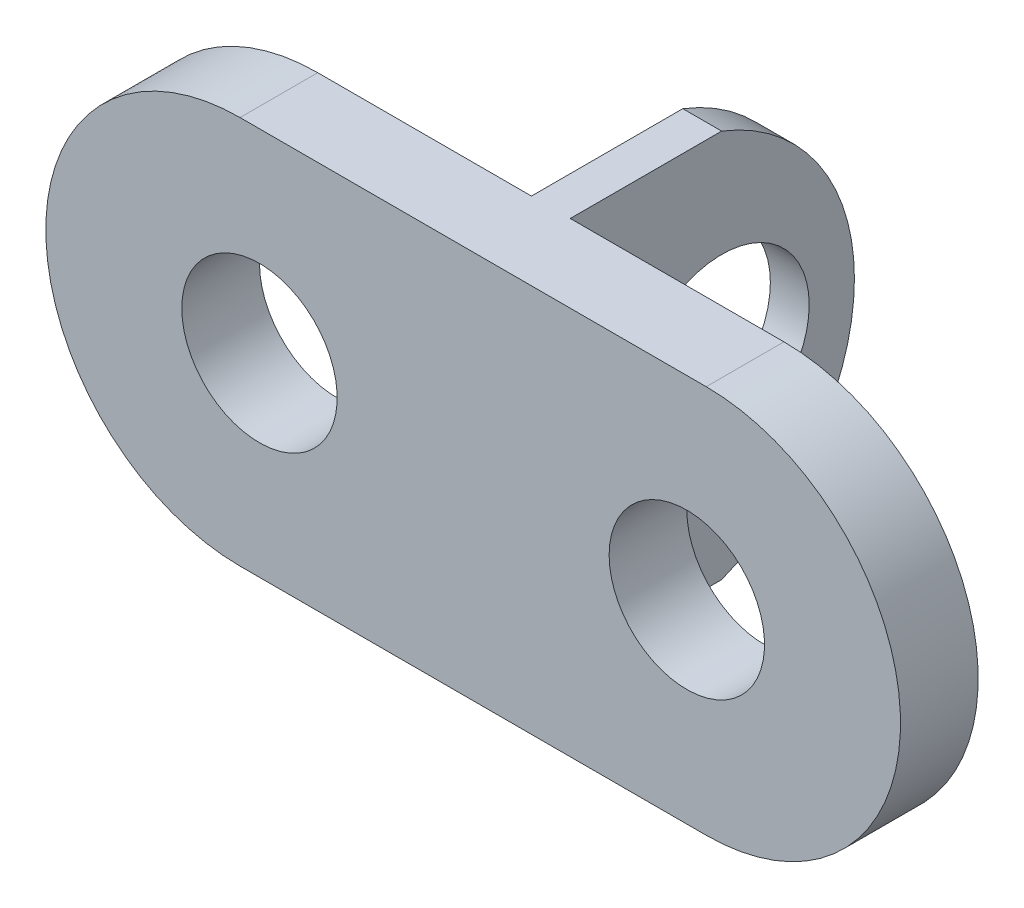
SolidWorks part; units mm, degrees
ref_plane "Front Plane" through (0, 0, 0) normal (0, 0, 1) x (1, 0, 0)
ref_plane "Top Plane" through (0, 0, 0) normal (0, 1, 0) x (1, 0, 0)
ref_plane "Right Plane" through (0, 0, 0) normal (1, 0, 0) x (0, 0, -1)
sketch "Esquisse1" plane through (0, 0, 0) normal (0, 0, 1) x (1, 0, 0)
  line L0 (-2.7952, 5.0683) -> (21.2048, 5.0683)
  line L1 (-2.7952, -14.9317) -> (21.2048, -14.9317)
  arc A0 (-2.7952, 5.0683) -> (-2.7952, -14.9317) centre (-2.7952, -4.9317) ccw
  arc A1 (21.2048, 5.0683) -> (21.2048, -14.9317) centre (21.2048, -4.9317) cw
  dimension "D2" = 10
  dimension "D1" = 24
  dimension "24" = 20
extrude "Boss.-Extru.1" add sketch "Esquisse1" along normal blind 4
sketch "Esquisse2" plane through (0, 0, 0) normal (0, 0, 1) x (1, 0, 0)
  line L0 (8.2048, 5.0683) -> (8.2048, -14.9317)
  line L1 (21.2048, 5.0683) -> (-2.7952, 5.0683) construction
  line L2 (-2.7952, -14.9317) -> (21.2048, -14.9317) construction
  line L3 (8.2048, -14.9317) -> (10.2048, -14.9317)
  line L4 (10.2048, -14.9317) -> (10.2048, 5.0683)
  line L5 (10.2048, 5.0683) -> (8.2048, 5.0683)
  dimension "D1" = 2
  dimension "D2" = 11
extrude "Boss.-Extru.2" add sketch "Esquisse2" against normal blind 15
sketch "Esquisse3" plane through (10.2048, 0, 0) normal (1, 0, 0) x (0, 0, -1)
  line L1 (15, 5.0683) -> (0, 5.0683) construction
  line L2 (15, -14.9317) -> (15, 5.0683) construction
  line L3 (0, 5.0683) -> (15, 5.0683)
  line L4 (0, 11) -> (0, -11) construction
  line L5 (15, 5.0683) -> (15, -14.9317)
  line L6 (15, -14.9317) -> (0, -14.9317)
  line L7 (15, -14.9317) -> (0, -14.9317) construction
  circle A0 centre (7.8, -4.9317) radius 4.5
  arc A2 (0, 5.0683) -> (0, -14.9317) centre (3.8962, -4.9317) cw
  line M3 (15, -14.9317) -> (15, 5.0683)
  line M4 (15, 5.0683) -> (0, 5.0683)
  dimension "D1" = 9
  dimension "D2" = 10
  dimension "7.2" = 7.2
extrude "Enlèv. mat.-Extru.1" cut sketch "Esquisse3" against normal through all contours A0 | A2 L6 M3 M4
sketch "Esquisse4" plane through (0, 0, 0) normal (0, 0, -1) x (-1, 0, 0)
  line L1 (-21.2048, 5.0683) -> (-10.2048, 5.0683) construction
  line L3 (-10.2048, -14.9317) -> (-10.2048, 5.0683) construction
  circle A1 centre (-20.2048, -4.9317) radius 4
  dimension "D1" = 8
  dimension "D2" = 10
  dimension "D3" = 10
extrude "Enlèv. mat.-Extru.2" cut sketch "Esquisse4" against normal through all
pattern_linear "Répétition linéaire1" count 2 spacing 22 along (-1, 0, 0) of "Enlèv. mat.-Extru.2"
